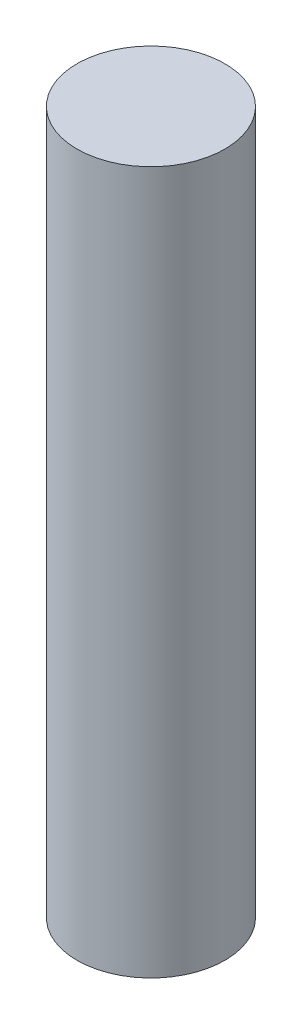
SolidWorks part; units mm, degrees
ref_plane "Front Plane" through (0, 0, 0) normal (0, 0, 1) x (1, 0, 0)
ref_plane "Top Plane" through (0, 0, 0) normal (0, 1, 0) x (1, 0, 0)
ref_plane "Right Plane" through (0, 0, 0) normal (1, 0, 0) x (0, 0, -1)
sketch "Sketch1" plane through (0, 0, 0) normal (0, 1, 0) x (1, 0, 0)
  circle A0 centre (0, 0) radius 1
  dimension "D1" = 2
extrude "Boss-Extrude1" add sketch "Sketch1" along normal blind 9.5
